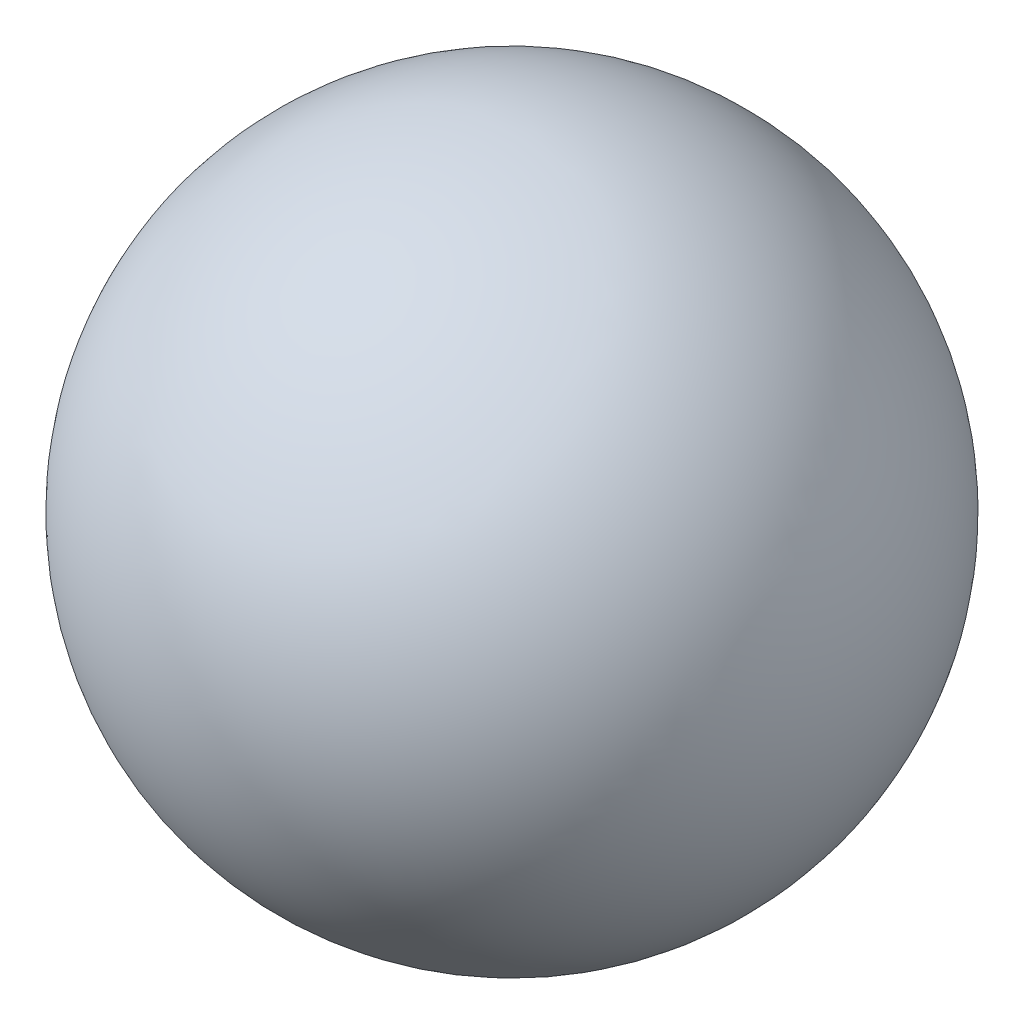
SolidWorks part; units mm, degrees
ref_plane "Plan1" through (0, 0, 0) normal (0, 0, 1) x (1, 0, 0)
ref_plane "Plan2" through (0, 0, 0) normal (0, 1, 0) x (1, 0, 0)
ref_plane "Plan3" through (0, 0, 0) normal (1, 0, 0) x (0, 0, -1)
sketch "Esquisse1" plane through (0, 0, 0) normal (0, 0, 1) x (1, 0, 0)
  line L0 (1, 4.25) -> (4, 4.25)
  line L1 (2.5, 4.25) -> (6.2305, 4.25) construction
  circle A0 centre (2.5, 4.25) radius 1.5 construction
  arc A1 (4, 4.25) -> (1, 4.25) centre (2.5, 4.25) ccw
revolve "Base-Révolution" add sketch "Esquisse1" angle 360 about L1
